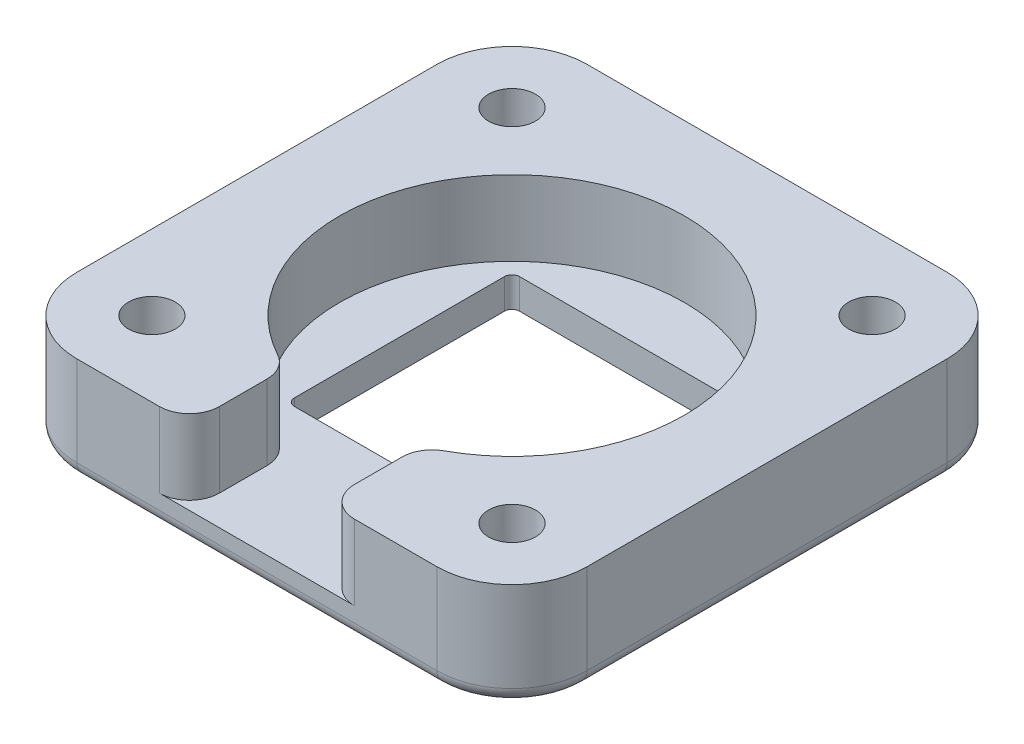
SolidWorks part; units mm, degrees
ref_plane "Front Plane" through (0, 0, 0) normal (0, 0, 1) x (1, 0, 0)
ref_plane "Top Plane" through (0, 0, 0) normal (0, 1, 0) x (1, 0, 0)
ref_plane "Right Plane" through (0, 0, 0) normal (1, 0, 0) x (0, 0, -1)
sketch "Sketch1" plane through (0, 0, 0) normal (0, 1, 0) x (1, 0, 0)
  line L1 (-17.6093, 13.1991) -> (16.3907, 13.1991)
  line L2 (-17.6093, 13.1991) -> (-17.6093, -20.8009)
  line L3 (-17.6093, -20.8009) -> (16.3907, -20.8009)
  line L4 (16.3907, 13.1991) -> (16.3907, -20.8009)
  dimension "D1" = 34
  dimension "D2" = 34
extrude "Boss-Extrude1" add sketch "Sketch1" along normal blind 7
sketch "Sketch2" plane through (0, 7, 0) normal (0, 1, 0) x (1, 0, 0)
  line L0 (-0.6093, 13.1991) -> (-0.6093, -34.5004) construction
  line L1 (16.3907, 13.1991) -> (-17.6093, 13.1991) construction
  line L2 (-17.6093, -3.8009) -> (26.5191, -3.8009) construction
  line L4 (-17.6093, 13.1991) -> (-17.6093, -20.8009) construction
  circle A0 centre (-0.6093, -3.8009) radius 11.5
  point P7 (-0.6093, -3.8009)
  dimension "D1" = 23
extrude "Cut-Extrude1" cut sketch "Sketch2" against normal blind 5
sketch "Sketch3" plane through (0, 7, 0) normal (0, 1, 0) x (1, 0, 0)
  line L0 (16.3907, 13.1991) -> (-17.6093, 13.1991) construction
  line L3 (-17.6093, 13.1991) -> (-17.6093, -20.8009) construction
  line L4 (-0.6093, 13.1991) -> (-0.6093, -21.9345) construction
  line L5 (-17.6093, -3.8009) -> (18.9364, -3.8009) construction
  circle A0 centre (-12.6093, 8.1991) radius 1.5621
  circle A1 centre (-12.6093, -15.8009) radius 1.5621
  circle A2 centre (11.3907, -15.8009) radius 1.5621
  circle A3 centre (11.3907, 8.1991) radius 1.5621
  dimension "D1" = 5
  dimension "D2" = 5
extrude "Cut-Extrude2" cut sketch "Sketch3" against normal through all
sketch "Sketch4" plane through (0, 7, 0) normal (0, 1, 0) x (1, 0, 0)
  line L0 (-0.6093, 13.1991) -> (-0.6093, -22.9594) construction
  line L1 (16.3907, 13.1991) -> (-17.6093, 13.1991) construction
  line L3 (-5.1093, -10.3426) -> (3.8907, -10.3426)
  line L4 (-5.1093, -10.3426) -> (-5.1093, -23.2421)
  line L5 (-5.1093, -23.2421) -> (3.8907, -23.2421)
  line L6 (3.8907, -10.3426) -> (3.8907, -23.2421)
  dimension "D1" = 9
  dimension "D2" = 4.5
extrude "Cut-Extrude3" cut sketch "Sketch4" against normal blind 5
sketch "Sketch5" plane through (0, 0, 0) normal (0, -1, 0) x (1, 0, 0)
  circle A0 centre (-12.6093, 15.8009) radius 2.6
  circle A1 centre (11.3907, 15.8009) radius 2.6
  circle A2 centre (-12.6093, -8.1991) radius 2.6
  circle A3 centre (11.3907, -8.1991) radius 2.6
extrude "Cut-Extrude4" cut sketch "Sketch5" against normal blind 4
fillet "Fillet1" radius 5 4 edges at (16.3907, 3.5, 20.8009) (16.3907, 3.5, -13.1991) (-17.6093, 3.5, -13.1991) (-17.6093, 3.5, 20.8009)
fillet "Fillet2" radius 1 12 edges at (14.9262, 0, -11.7347) (-0.6093, 0, -13.1991) (-16.1449, 0, -11.7347) (-17.6093, 0, 3.8009) (-16.1449, 0, 19.3364) (-0.6093, 0, 20.8009) (14.9262, 0, 19.3364) (16.3907, 0, 3.8009) (-12.6093, 0, 13.2009) (11.3907, 0, -10.7991) (-12.6093, 0, -10.7991) (11.3907, 0, 13.2009)
fillet "Fillet3" radius 2 4 edges at (-5.1093, 4.5, 14.3839) (3.8907, 4.5, 14.3839) (-5.1093, 4.5, 20.8009) (3.8907, 4.5, 20.8009)
sketch "Sketch6" plane through (0, 0, 0) normal (0, -1, 0) x (1, 0, 0)
  line L0 (-0.6093, 19.8009) -> (-0.6093, -12.1991) construction
  line L1 (11.3907, 19.8009) -> (-12.6093, 19.8009) construction
  line L2 (-12.6093, -12.1991) -> (11.3907, -12.1991) construction
  line L3 (-16.6093, 3.8009) -> (15.3907, 3.8009) construction
  line L4 (-16.6093, 15.8009) -> (-16.6093, -8.1991) construction
  line L5 (15.3907, -8.1991) -> (15.3907, 15.8009) construction
  line L7 (-8.1093, 11.3009) -> (6.8907, 11.3009)
  line L8 (-8.1093, 11.3009) -> (-8.1093, -3.6991)
  line L9 (-8.1093, -3.6991) -> (6.8907, -3.6991)
  line L10 (6.8907, 11.3009) -> (6.8907, -3.6991)
  dimension "D1" = 15
  dimension "D2" = 15
  dimension "D3" = 7.5
  dimension "D4" = 7.5
extrude "Cut-Extrude5" cut sketch "Sketch6" against normal blind 2
sketch "Sketch7" plane through (0, 2, 0) normal (0, 1, 0) x (1, 0, 0)
  line L0 (6.8907, -3.8009) -> (-8.1093, -3.8009) construction
  line L1 (6.8907, 3.6991) -> (6.8907, -11.3009) construction
  line L2 (-8.1093, -11.3009) -> (-8.1093, 3.6991) construction
  line L3 (-0.6093, -11.3009) -> (-0.6093, 3.6991) construction
  line L4 (6.8907, -11.3009) -> (-8.1093, -11.3009) construction
  line L5 (-8.1093, 3.6991) -> (6.8907, 3.6991) construction
  line L6 (8.8907, -3.8009) -> (-10.1093, -3.8009) construction
  circle A0 centre (-0.6093, -3.8009) radius 9.5
  circle A1 centre (8.8907, -3.8009) radius 1.55
  circle A3 centre (-10.1093, -3.8009) radius 1.55
  circle A5 centre (-0.6093, -13.3009) radius 1.55
  circle A6 centre (-0.6093, 5.6991) radius 1.55
  point P12 (-0.6093, -3.8009)
  point P27 (-0.6093, -3.8009)
  dimension "D1" = 4
fillet "Fillet6" radius 0.5 4 edges at (-8.1093, 1, -3.6991) (6.8907, 1, -3.6991) (-8.1093, 1, 11.3009) (6.8907, 1, 11.3009)
